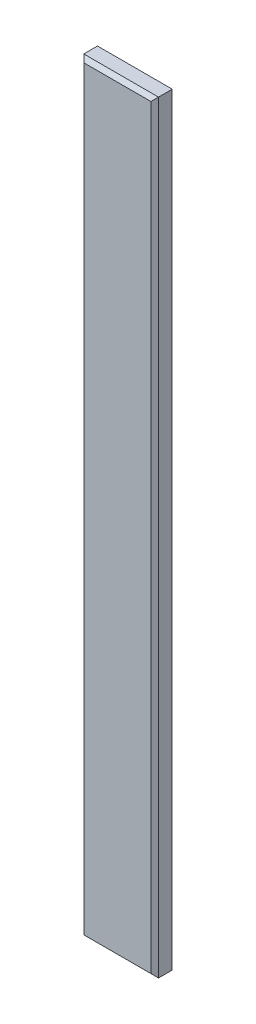
SolidWorks part; units mm, degrees
ref_plane "Front Plane" through (0, 0, 0) normal (0, 0, 1) x (1, 0, 0)
ref_plane "Top Plane" through (0, 0, 0) normal (0, 1, 0) x (1, 0, 0)
ref_plane "Right Plane" through (0, 0, 0) normal (1, 0, 0) x (0, 0, -1)
sketch "Sketch1" plane through (0, 0, 0) normal (0, 1, 0) x (1, 0, 0)
  line L1 (-4.9, 1.4) -> (4.9, 1.4)
  line L2 (-4.9, 1.4) -> (-4.9, -1.4)
  line L3 (-4.9, -1.4) -> (4.9, -1.4)
  line L4 (4.9, 1.4) -> (4.9, -1.4)
  line L5 (-4.9, 1.4) -> (4.9, -1.4) construction
  line L6 (-4.9, -1.4) -> (4.9, 1.4) construction
  point P0 (0, 0)
extrude "Boss-Extrude1" add sketch "Sketch1" along normal blind 100
chamfer "Chamfer1" distance 0.5 angle 45 8 edges at (-4.9, 50, 1.4) (0, 100, 1.4) (4.9, 50, 1.4) (0, 0, 1.4) (4.9, 50, -1.4) (0, 100, -1.4) (-4.9, 50, -1.4) (0, 0, -1.4)
